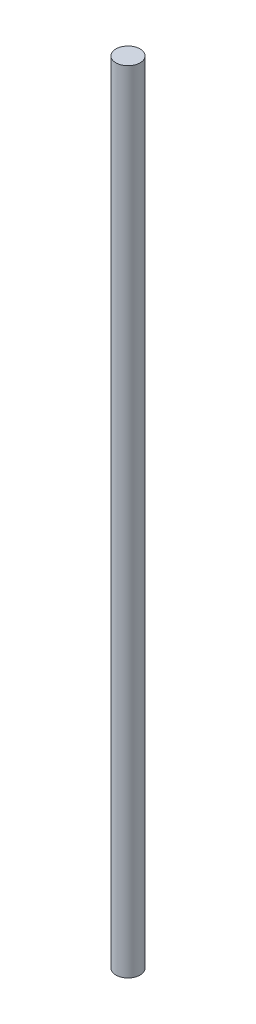
SolidWorks part; units mm, degrees
ref_plane "Front Plane" through (0, 0, 0) normal (0, 0, 1) x (1, 0, 0)
ref_plane "Top Plane" through (0, 0, 0) normal (0, 1, 0) x (1, 0, 0)
ref_plane "Right Plane" through (0, 0, 0) normal (1, 0, 0) x (0, 0, -1)
sketch "Sketch1" plane through (0, 0, 0) normal (0, 1, 0) x (1, 0, 0)
  circle A0 centre (0, 0) radius 10
  dimension "D1" = 20
extrude "Boss-Extrude1" add sketch "Sketch1" along normal blind 654
cosmetic thread "Cosmetic Thread1"
